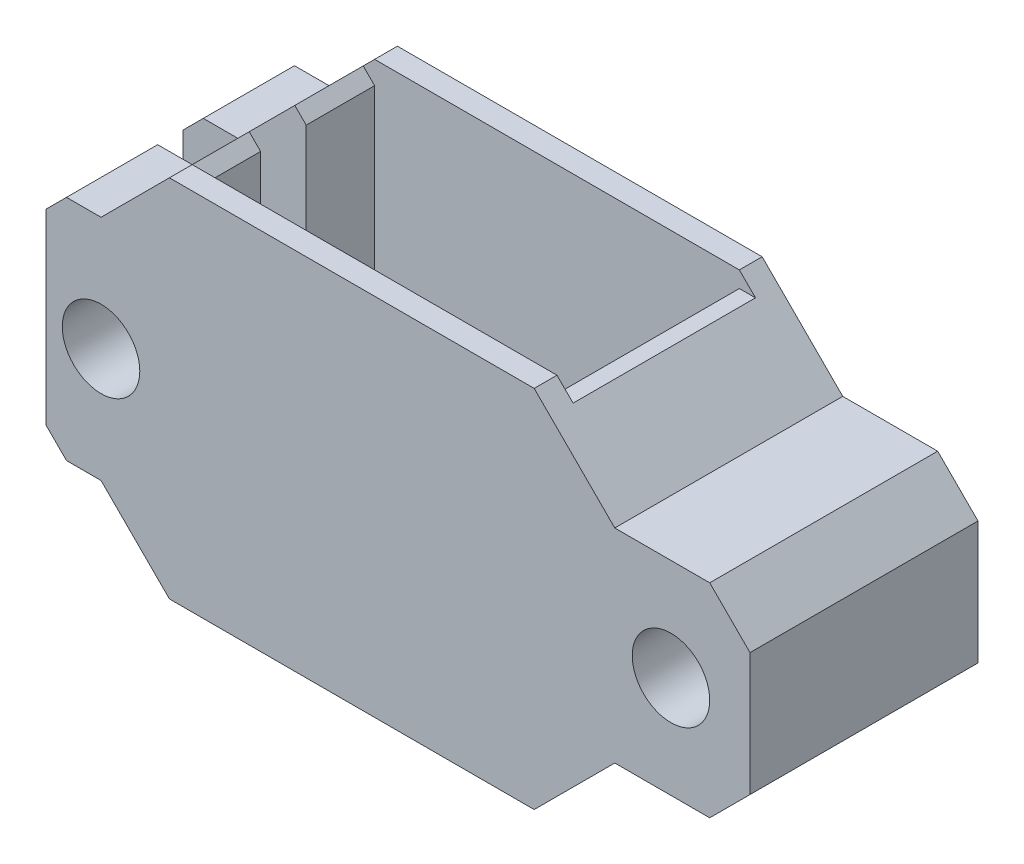
SolidWorks part; units mm, degrees
ref_plane "Front Plane" through (0, 0, 0) normal (0, 0, 1) x (1, 0, 0)
ref_plane "Top Plane" through (0, 0, 0) normal (0, 1, 0) x (1, 0, 0)
ref_plane "Right Plane" through (0, 0, 0) normal (1, 0, 0) x (0, 0, -1)
sketch "Sketch1" plane through (0, 0, 0) normal (0, 0, 1) x (1, 0, 0)
  line L2 (0, -8) -> (-16, -8)
  line L4 (-16, 8) -> (0, 8)
  line L13 (0, 8) -> (3.5355, 4.4645)
  line L14 (0, -8) -> (3.5355, -4.4645)
  line L15 (3.5355, 4.4645) -> (6, 4.4645)
  line L16 (3.5355, -4.4645) -> (6, -4.4645)
  line L17 (6, -4.4645) -> (7.7, -4.4645)
  line L18 (7.7, -4.4645) -> (9.4678, -2.6967)
  line L19 (9.4678, 2.6967) -> (9.4678, -2.6967)
  line L20 (6, 4.4645) -> (7.7, 4.4645)
  line L21 (7.7, 4.4645) -> (9.4678, 2.6967)
  line L22 (-16, 8) -> (-19, 5)
  line L23 (-19, 5) -> (-20.5153, 5)
  line L24 (-20.5153, 5) -> (-21.4138, 4.1015)
  line L25 (-21.4138, 4.1015) -> (-21.4138, -1.5357)
  line L26 (-16, -8) -> (-19, -5)
  line L27 (-19, -5) -> (-20.5153, -5)
  line L28 (-20.5153, -5) -> (-21.4138, -4.1015)
  line L29 (-21.4138, -4.1015) -> (-21.4138, -1.5357)
  circle A0 centre (6, 0) radius 1.7
  circle A1 centre (-19, 0) radius 1.25
extrude "Boss-Extrude1" add sketch "Sketch1" along normal blind 5
sketch "Sketch11" plane through (0, 0, 5) normal (0, 0, 1) x (1, 0, 0)
  line L1 (-16, 8) -> (0, 8)
  line L2 (-16, 8) -> (-16, -8)
  line L3 (-16, -8) -> (0, -8)
  line L4 (0, 8) -> (0, -8)
extrude "Cut-Extrude6" cut sketch "Sketch11" against normal blind 4
sketch "Sketch13" plane through (0, 0, 5) normal (0, 0, 1) x (1, 0, 0)
  line L1 (-16, 8) -> (-23.4238, 8)
  line L2 (-16, 8) -> (-16, -8.5299)
  line L3 (-16, -8.5299) -> (-23.4238, -8.5299)
  line L4 (-23.4238, 8) -> (-23.4238, -8.5299)
extrude "Cut-Extrude8" cut sketch "Sketch13" against normal blind 1
chamfer "Chamfer2" distance 1 angle 45 4 edges at (0, 8, 3) (-16, 8, 2.5) (0, -8, 3) (-16, -8, 2.5)
mirror "Mirror1" about plane through (0, 0, 5) normal (0, 0, -1) of bodies 109
sketch "Sketch15" plane through (0, 0, 10) normal (0, 0, 1) x (1, 0, 0)
  circle A0 centre (-19, 0) radius 1.7
extrude "Cut-Extrude9" cut sketch "Sketch15" against normal blind 5
